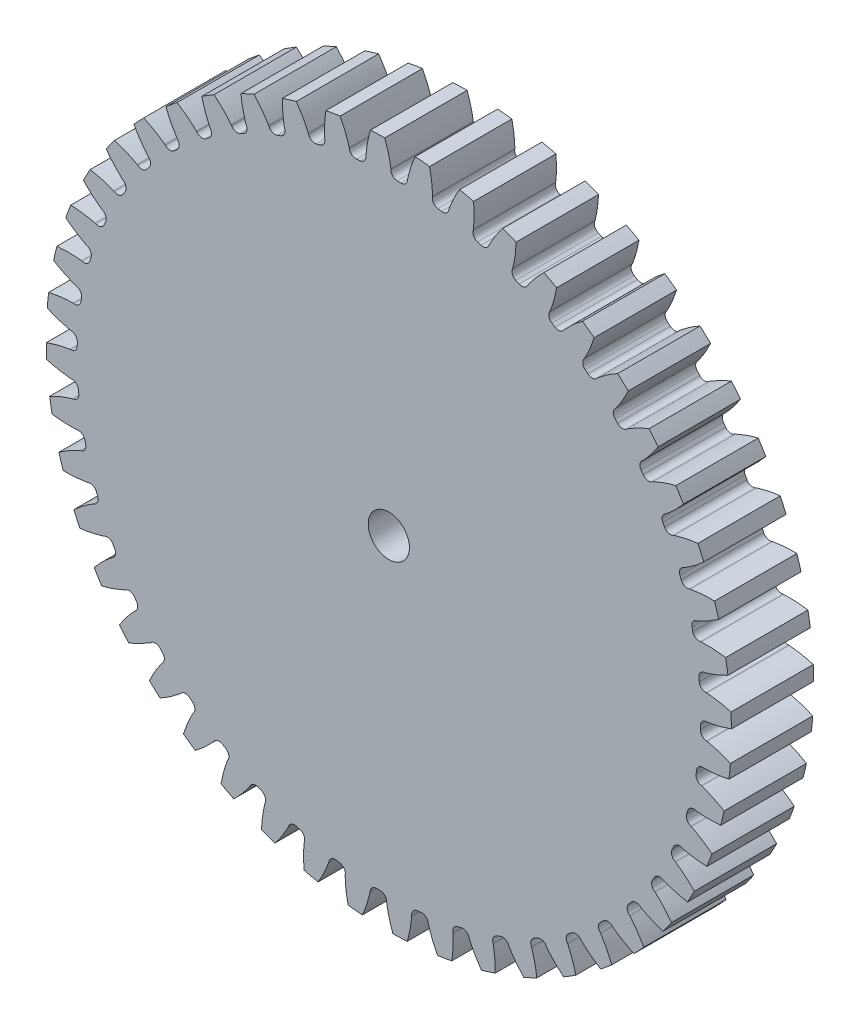
SolidWorks part; units mm, degrees
ref_plane "Front" through (0, 0, 0) normal (0, 0, 1) x (1, 0, 0)
ref_plane "Top" through (0, 0, 0) normal (0, 1, 0) x (1, 0, 0)
ref_plane "Right" through (0, 0, 0) normal (1, 0, 0) x (0, 0, -1)
sketch "Sketch1" plane through (0, 0, 0) normal (0, 0, 1) x (1, 0, 0)
  line L0 (-609.6, 0) -> (609.6, 0) construction
  circle A0 centre (0, 0) radius 26.416
  circle A1 centre (0, 0) radius 25.4 construction
  circle A3 centre (0, 0) radius 24.0348 construction
  dimension "D3" = 1.016
  dimension "D1" = 2.3812
extrude "Boss-Extrude1" add sketch "Sketch1" against normal blind 6.35
sketch "Sketch3" plane through (0, 0, 0) normal (0, 0, 1) x (1, 0, 0)
  line L0 (0, 0) -> (0, 26.416) construction
  line L1 (-6.1571, 23.8077) -> (0, 25.4)
  line L2 (-9.5921, 25.4) -> (9.5921, 25.4) construction
  line L3 (-9.2865, 22.9983) -> (9.2865, 27.8017) construction
  line L4 (-6.1571, 23.8077) -> (0, 0) construction
  line L5 (-15.7046, 18.923) -> (0, 0) construction
  line L6 (-15.7046, 18.923) -> (-2.5109, 29.8728) construction
  line L7 (-4.2933, 24.2133) -> (0, 0) construction
  line L8 (-4.2933, 24.2133) -> (0.0901, 24.9905) construction
  arc A0 (-6.1571, 23.8077) -> (-15.7046, 18.923) centre (0, 0) ccw
  circle A1 centre (0, 0) radius 25.4 construction
  circle A2 centre (0, 0) radius 24.591 construction
  arc A3 (-6.1571, 23.8077) -> (-4.2933, 24.2133) centre (0, 0) cw
  circle A4 centre (0, 0) radius 26.416 construction
  point P6 (0, 25.4)
  dimension "D1" = 6.3597
  dimension "Pressure Angle" = 14.5
  dimension "D2" = 10.8114
  dimension "D3" = 17.1457
  dimension "D4" = 1.9079
  dimension "D5" = 4.4518
sketch "Sketch4" plane through (0, 0, 0) normal (0, 0, 1) x (1, 0, 0)
  line L0 (0, 0) -> (0.8306, 25.3728) construction
  line L1 (0.16, 24.5904) -> (0.16, 24.0342)
  line L2 (0, 25.4) -> (1.6612, 25.3456) construction
  line L3 (1.4487, 24.5482) -> (1.4123, 23.9932)
  line L4 (0.16, 24.0342) -> (0, 0) construction
  line L5 (0, 0) -> (0, 26.416) construction
  line L6 (-15.7046, 18.923) -> (-2.5109, 29.8728) construction
  line L7 (-15.7046, 18.923) -> (-2.5109, 29.8728) construction
  arc A0 (1.4123, 23.9932) -> (0.16, 24.0342) centre (0, 0) ccw
  arc A1 (0, 25.4) -> (1.6612, 25.3456) centre (0, 0) cw construction
  circle A2 centre (0, 0) radius 25.4 construction
  circle A3 centre (0, 0) radius 24.591 construction
  circle A4 centre (0, 0) radius 24.0348 construction
  arc A5 (4.4593, 29.6446) -> (-2.5109, 29.8728) centre (0, 0) ccw
  spline S0 degree 2 poles (-2.5109, 29.8728) (-0.2902, 27.536) (0.16, 24.5904) knots 0 0 0 1 1 1
  spline S1 degree 2 poles (4.4593, 29.6446) (2.0905, 27.4581) (1.4487, 24.5482) knots 0 0 0 1 1 1
  dimension "D1" = 1.6624
extrude "Cut-Extrude1" cut sketch "Sketch4" against normal through all
fillet "Fillet1" radius 0.4987 2 edges at (1.4123, 23.9932, -3.175) (0.16, 24.0342, -3.175)
pattern_circular "CirPattern1" count 48 over 360 about axis through (0, 0, -6.35) along (0, 0, 1) of "Cut-Extrude1", "Fillet1"
sketch "Sketch5" plane through (0, 0, 0) normal (0, 0, 1) x (1, 0, 0)
  line L0 (0, 5.9538) -> (0, 0) construction
  circle A0 centre (0, 0) radius 1.5875
  point P9 (0, -1.5875)
  dimension "Bore Min" = 3.175
extrude "Cut-Extrude2" cut sketch "Sketch5" against normal through all
equation "\"D1@Sketch4\" = 1.5708/(\"Number of Teeth@Sketch1\"/\"Ptich Dia@Sketch1\")"
equation "\"D1@CirPattern1\" = \"Number of Teeth@Sketch1\""
equation "\"D1@Fillet1\" = \"D1@Sketch4\"*.3"
equation "\"D1@Sketch1\" = 2.250/(\"Number of Teeth@Sketch1\"/\"Ptich Dia@Sketch1\")"
